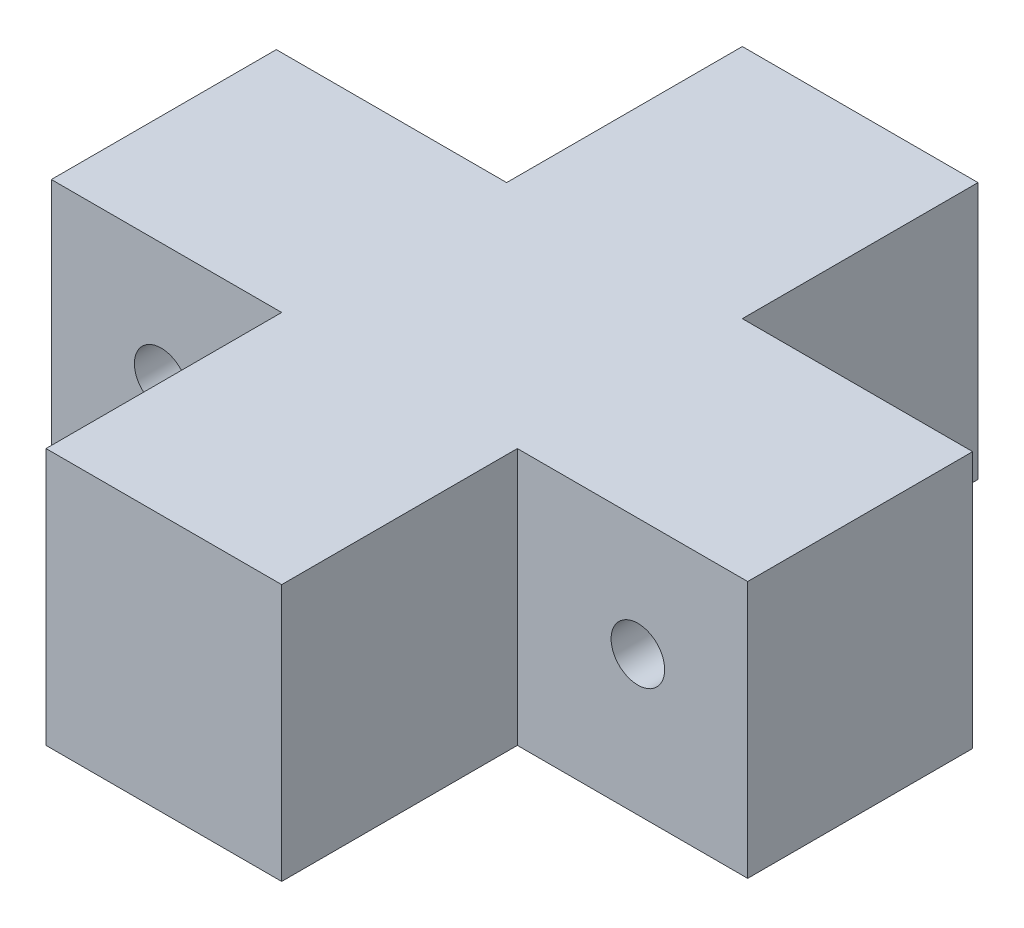
SolidWorks part; units mm, degrees
ref_plane "Front" through (0, 0, 0) normal (0, 0, 1) x (1, 0, 0)
ref_plane "Top" through (0, 0, 0) normal (0, 1, 0) x (1, 0, 0)
ref_plane "Right" through (0, 0, 0) normal (1, 0, 0) x (0, 0, -1)
sketch "Sketch1" plane through (0, 0, 0) normal (0, 1, 0) x (1, 0, 0)
  line L1 (-32.5, 32.5) -> (32.5, 32.5)
  line L2 (-32.5, 32.5) -> (-32.5, -32.5)
  line L3 (-32.5, -32.5) -> (32.5, -32.5)
  line L4 (32.5, 32.5) -> (32.5, -32.5)
  line L5 (-32.5, 32.5) -> (32.5, -32.5) construction
  line L6 (-32.5, -32.5) -> (32.5, 32.5) construction
  point P0 (0, 0)
  dimension "D1" = 65
  dimension "D2" = 65
extrude "Boss-Extrude1" add sketch "Sketch1" along normal blind 24
sketch "Sketch3" plane through (0, 24, 0) normal (0, 1, 0) x (1, 0, 0)
  line L0 (-32.5, 10.5) -> (-11, 10.5)
  line L1 (-32.5, 32.5) -> (-32.5, -32.5) construction
  line L2 (-11, 10.5) -> (-11, 32.5)
  line L3 (32.5, 32.5) -> (-32.5, 32.5) construction
  line L4 (-11, 32.5) -> (-32.5, 32.5)
  line L5 (-32.5, 32.5) -> (-32.5, 10.5)
  line L6 (0, -50) -> (0, 50) construction
  line L7 (32.5, 32.5) -> (32.5, 10.5)
  line L8 (11, 32.5) -> (32.5, 32.5)
  line L9 (11, 10.5) -> (11, 32.5)
  line L10 (32.5, 10.5) -> (11, 10.5)
  line L11 (-50, 0) -> (50, 0) construction
  line L12 (32.5, -10.5) -> (11, -10.5)
  line L13 (11, -10.5) -> (11, -32.5)
  line L14 (11, -32.5) -> (32.5, -32.5)
  line L15 (32.5, -32.5) -> (32.5, -10.5)
  line L16 (-32.5, -32.5) -> (-32.5, -10.5)
  line L17 (-11, -32.5) -> (-32.5, -32.5)
  line L18 (-11, -10.5) -> (-11, -32.5)
  line L19 (-32.5, -10.5) -> (-11, -10.5)
  dimension "D1" = 11
  dimension "D2" = 22
extrude "Cut-Extrude2" cut sketch "Sketch3" against normal through all
sketch "Sketch4" plane through (0, 0, 0) normal (0, 0, 1) x (1, 0, 0)
  line L0 (-11, 0) -> (11, 0) construction
  line L2 (0, -50) -> (0, 50) construction
  line L5 (-11, 24) -> (-32.5, 24) construction
  circle A0 centre (-22.25, 13) radius 2.5
  circle A1 centre (22.25, 13) radius 2.5
  point P4 (0, 0)
  point P5 (0, 0)
  point P7 (-19.286, 9.5974)
  point P14 (-22.25, 9.8177)
  dimension "D1" = 5
  dimension "D2" = 22.25
  dimension "D3" = 11
extrude "Cut-Extrude3" cut sketch "Sketch4" against normal through all both and the other way through all
